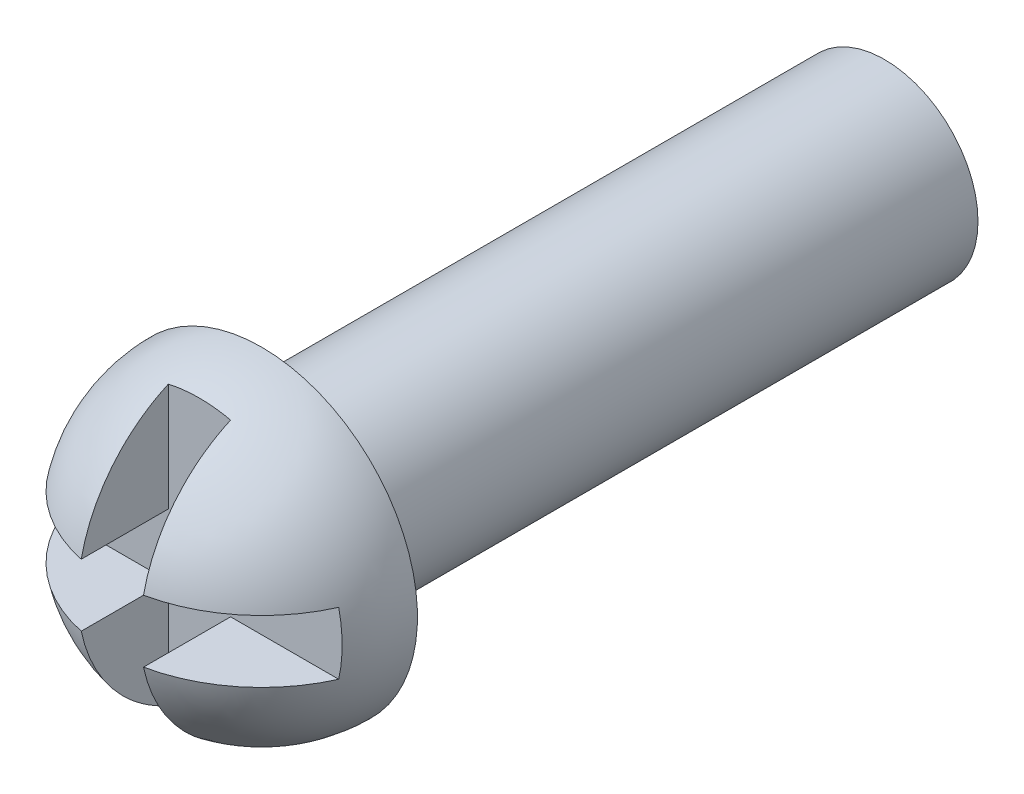
SolidWorks part; units mm, degrees
ref_plane "Front Plane" through (0, 0, 0) normal (0, 0, 1) x (1, 0, 0)
ref_plane "Top Plane" through (0, 0, 0) normal (0, 1, 0) x (1, 0, 0)
ref_plane "Right Plane" through (0, 0, 0) normal (1, 0, 0) x (0, 0, -1)
sketch "Sketch1" plane through (0, 0, 0) normal (0, 0, 1) x (1, 0, 0)
  circle A0 centre (0, 0) radius 1.5
  dimension "D1" = 3
extrude "Boss-Extrude1" add sketch "Sketch1" along normal blind 10
sketch "Sketch2" plane through (0, 0, 10) normal (0, 0, 1) x (1, 0, 0)
  line L0 (0, 2.5) -> (0, -2.5)
  arc A0 (0, -2.5) -> (0, 2.5) centre (0, 0) ccw
  dimension "D1" = 5
revolve "Revolve1" add sketch "Sketch2" angle 180 about L0
ref_plane "Plane1" through (0, 0, 13) normal (0, 0, 1) x (1, 0, 0)
sketch "Sketch3" plane through (0, 0, 13) normal (0, 0, 1) x (1, 0, 0)
  line L0 (0.5, 0.5) -> (3, 0.5)
  line L1 (-3, 0.5) -> (-0.5, 0.5)
  line L2 (-3, 0.5) -> (-3, -0.5)
  line L3 (-3, -0.5) -> (-0.5, -0.5)
  line L4 (3, 0.5) -> (3, -0.5)
  line L5 (-0.5, 2.9294) -> (0.5, 2.9294)
  line L6 (-0.5, 2.9294) -> (-0.5, 0.5)
  line L7 (-0.5, -3.0706) -> (0.5, -3.0706)
  line L8 (0.5, 2.9294) -> (0.5, 0.5)
  line L9 (0.5, -0.5) -> (0.5, -3.0706)
  line L10 (0.5, -0.5) -> (3, -0.5)
  line L11 (-0.5, -0.5) -> (-0.5, -3.0706)
  dimension "D1" = 6
  dimension "D2" = 1
  dimension "D3" = 0.5
  dimension "D4" = 3
  dimension "D5" = 0.5
  dimension "D6" = 6
  dimension "D7" = 1
extrude "Cut-Extrude1" cut sketch "Sketch3" against normal blind 2
